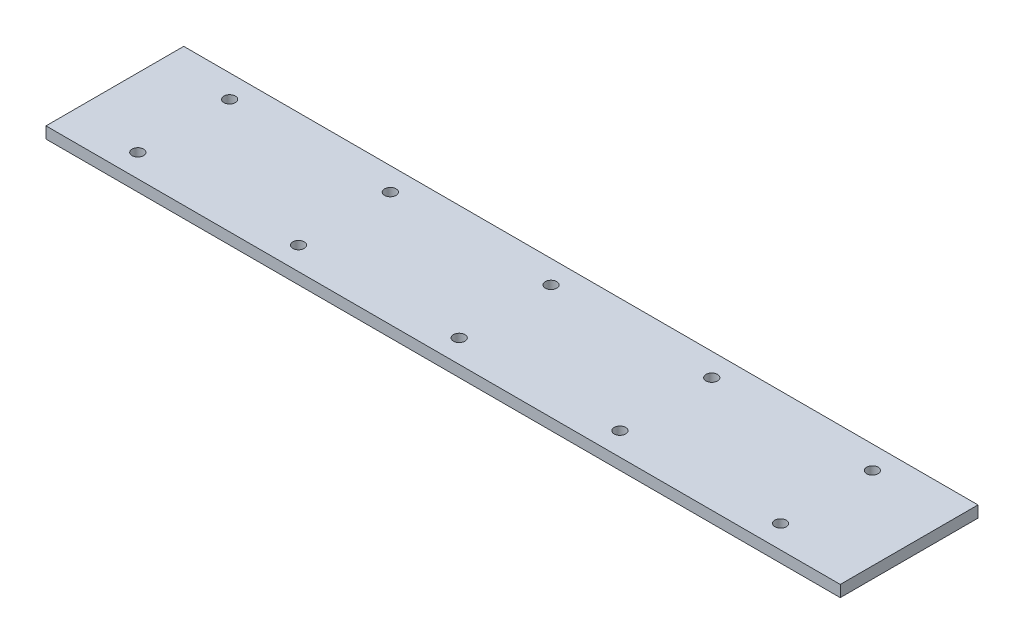
SolidWorks part; units mm, degrees
ref_plane "Front Plane" through (0, 0, 0) normal (0, 0, 1) x (1, 0, 0)
ref_plane "Top Plane" through (0, 0, 0) normal (0, 1, 0) x (1, 0, 0)
ref_plane "Right Plane" through (0, 0, 0) normal (1, 0, 0) x (0, 0, -1)
sketch "Sketch1" plane through (0, 0, 0) normal (0, 1, 0) x (1, 0, 0)
  line L0 (0, 60) -> (0, 50) construction
  line L1 (0, 0) -> (346, 0)
  line L2 (0, 0) -> (0, 60)
  line L3 (0, 60) -> (346, 60)
  line L4 (346, 0) -> (346, 60)
  line L5 (0, 50) -> (30, 50) construction
  line L6 (30, 50) -> (100, 50) construction
  line L7 (100, 50) -> (170, 50) construction
  line L8 (170, 50) -> (240, 50) construction
  line L9 (240, 50) -> (310, 50) construction
  line L10 (310, 50) -> (346, 50) construction
  line L11 (0, 30) -> (-35.1196, 30) construction
  line L12 (240, 10) -> (310, 10) construction
  line L13 (170, 10) -> (240, 10) construction
  line L14 (100, 10) -> (170, 10) construction
  line L15 (30, 10) -> (100, 10) construction
  line L16 (0, 10) -> (30, 10) construction
  line L17 (0, 0) -> (0, 10) construction
  circle A0 centre (30, 50) radius 2.5
  circle A1 centre (100, 50) radius 2.5
  circle A2 centre (170, 50) radius 2.5
  circle A3 centre (240, 50) radius 2.5
  circle A4 centre (310, 50) radius 2.5
  circle A5 centre (310, 10) radius 2.5
  circle A6 centre (240, 10) radius 2.5
  circle A7 centre (170, 10) radius 2.5
  circle A8 centre (100, 10) radius 2.5
  circle A9 centre (30, 10) radius 2.5
extrude "Boss-Extrude1" add sketch "Sketch1" along normal blind 5
